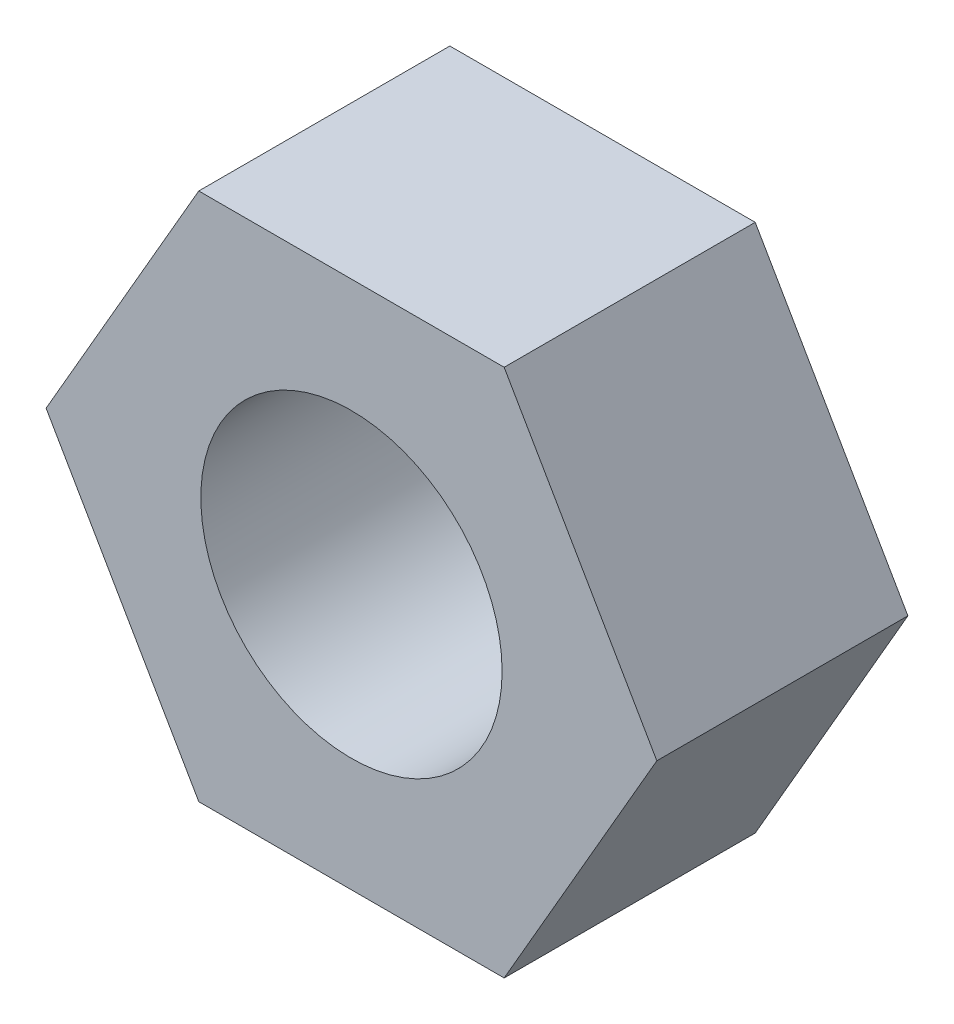
SolidWorks part; units mm, degrees
ref_plane "Front" through (0, 0, 0) normal (0, 0, 1) x (1, 0, 0)
ref_plane "Top" through (0, 0, 0) normal (0, 1, 0) x (1, 0, 0)
ref_plane "Right" through (0, 0, 0) normal (1, 0, 0) x (0, 0, -1)
sketch "Sketch1" plane through (0, 0, 0) normal (0, 0, 1) x (1, 0, 0)
  line L1 (2.2805, 3.95) -> (-2.2805, 3.95)
  line L2 (-2.2805, 3.95) -> (-4.5611, 0)
  line L3 (-4.5611, 0) -> (-2.2805, -3.95)
  line L4 (-2.2805, -3.95) -> (2.2805, -3.95)
  line L5 (2.2805, -3.95) -> (4.5611, 0)
  line L6 (4.5611, 0) -> (2.2805, 3.95)
  circle A0 centre (0, 0) radius 3.95 construction
  dimension "D1" = 7.9
extrude "Boss-Extrude1" add sketch "Sketch1" along normal blind 3.75
sketch "Sketch2" plane through (0, 0, 3.75) normal (0, 0, 1) x (1, 0, 0)
  circle A0 centre (0, 0) radius 2.25
  dimension "D1" = 4.5
extrude "Cut-Extrude1" cut sketch "Sketch2" against normal through all
